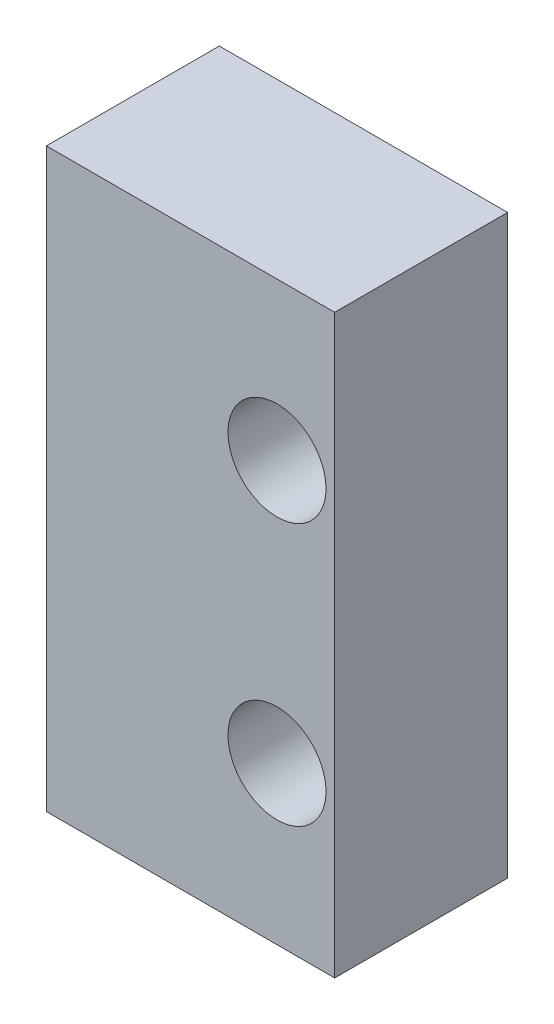
SolidWorks part; units mm, degrees
ref_plane "Plan de face" through (0, 0, 0) normal (0, 0, 1) x (1, 0, 0)
ref_plane "Plan de dessus" through (0, 0, 0) normal (0, 1, 0) x (1, 0, 0)
ref_plane "Plan de droite" through (0, 0, 0) normal (1, 0, 0) x (0, 0, -1)
sketch "Esquisse1" plane through (0, 0, 0) normal (0, 0, 1) x (1, 0, 0)
  line L0 (3.3, 0) -> (-3.3, 0) construction
  line L1 (-5, -10) -> (5, -10)
  line L2 (-5, -10) -> (-5, 10)
  line L3 (-5, 10) -> (5, 10)
  line L4 (5, -10) -> (5, 10)
  line L5 (-5, -10) -> (5, 10) construction
  line L6 (-5, 10) -> (5, -10) construction
  circle A0 centre (3, 4.55) radius 1.7
  circle A1 centre (3, -4.55) radius 1.7
  point P0 (0, 0)
  dimension "D3" = 3.4
  dimension "D4" = 9.1
  dimension "D1" = 10
  dimension "D2" = 20
  dimension "D5" = 8
extrude "Boss.-Extru.1" add sketch "Esquisse1" along normal mid plane 6
